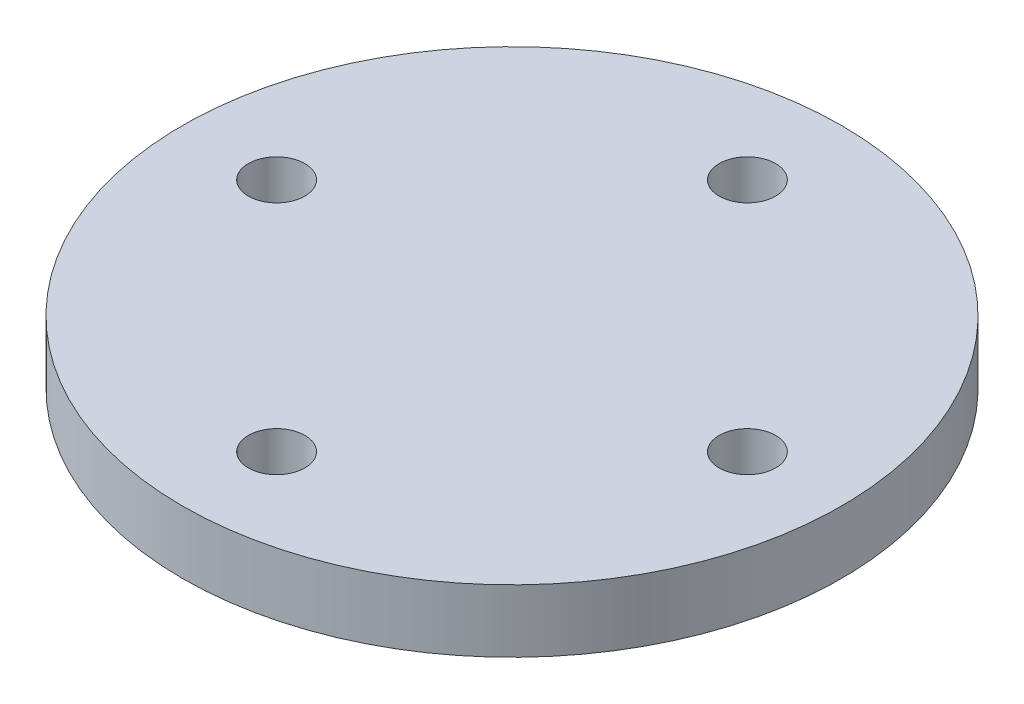
SolidWorks part; units mm, degrees
ref_plane "Спереди" through (0, 0, 0) normal (0, 0, 1) x (1, 0, 0)
ref_plane "Сверху" through (0, 0, 0) normal (0, 1, 0) x (1, 0, 0)
ref_plane "Справа" through (0, 0, 0) normal (1, 0, 0) x (0, 0, -1)
other "Configuration Table"
sketch "Эскиз1" plane through (0, 0, 0) normal (0, 1, 0) x (1, 0, 0)
  line L0 (19.7479, 352.9809) -> (75.2479, 352.9809) construction
  line L1 (-6.8249, 0) -> (8.076, 0) construction
  line L2 (0, 3.9658) -> (0, -3.3299) construction
  circle A0 centre (0, 0) radius 10.5
  circle A1 centre (0, -7.5) radius 0.9
  circle A2 centre (0, 7.5) radius 0.9
  circle A3 centre (-7.5, 0) radius 0.9
  circle A4 centre (7.5, 0) radius 0.9
  point P19 (0, 0)
  dimension "D1" = 21
  dimension "D3" = 1.8
  dimension "D2" = 55.5
  dimension "D4" = 2
  dimension "D5" = 7.5
  dimension "D6" = 7.5
  dimension "D7" = 7.5
  dimension "D8" = 7.5
extrude "Бобышка-Вытянуть1" add sketch "Эскиз1" along normal blind 2
